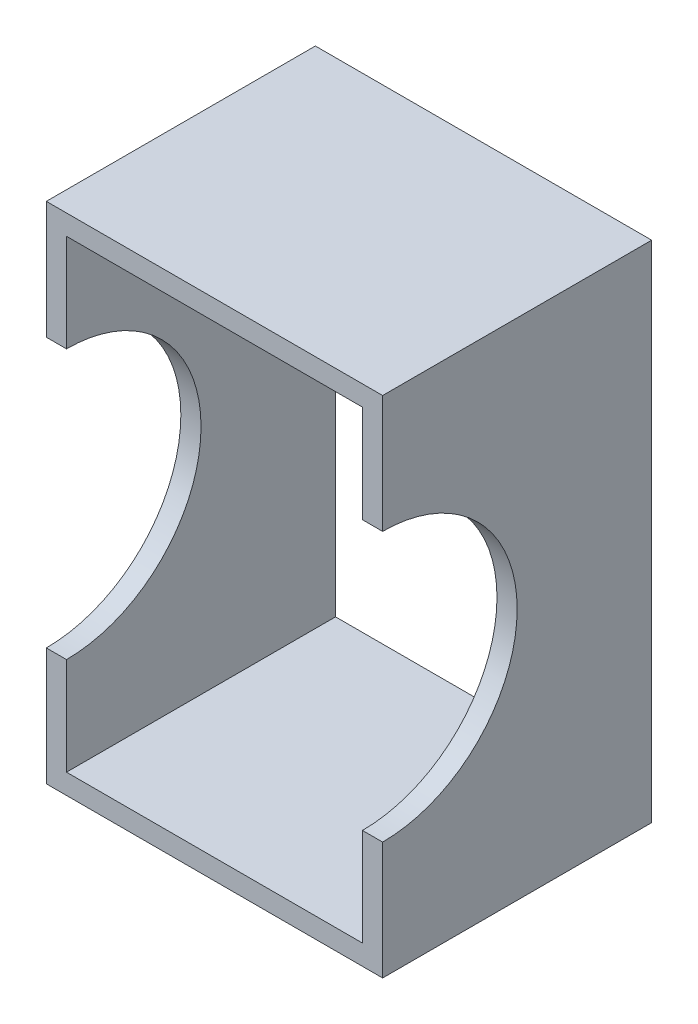
SolidWorks part; units mm, degrees
material "Plain Carbon Steel"
ref_plane "Front Plane" through (0, 0, 0) normal (0, 0, 1) x (1, 0, 0)
ref_plane "Top Plane" through (0, 0, 0) normal (0, 1, 0) x (1, 0, 0)
ref_plane "Right Plane" through (0, 0, 0) normal (1, 0, 0) x (0, 0, -1)
sketch "Sketch1" plane through (0, 0, 0) normal (0, 0, 1) x (1, 0, 0)
  line B0 (-50, -75) -> (50, -75)
  line B1 (-50, -75) -> (-50, 75)
  line B2 (50, -75) -> (50, 75)
  line B3 (-50, 75) -> (50, 75)
  line B4 (-44, -69) -> (44, -69)
  line B5 (-44, -69) -> (-44, 69)
  line B6 (44, -69) -> (44, 69)
  line B7 (-44, 69) -> (44, 69)
sketch_block_instance "15x10x6_profil-1"
sketch_block "15x10x6_profil" parameters "D1"=100, "D2"=150, "D3"=6, "D4"=6
extrude "Boss-Extrude1" add sketch "Sketch1" against normal blind 80
sketch "Sketch2" plane through (0, 0, 0) normal (1, 0, 0) x (0, 0, -1)
  circle A0 centre (0, 0) radius 40
  dimension "D1" = 80
extrude "Cut-Extrude1" cut sketch "Sketch2" against normal through all and the other way through all
